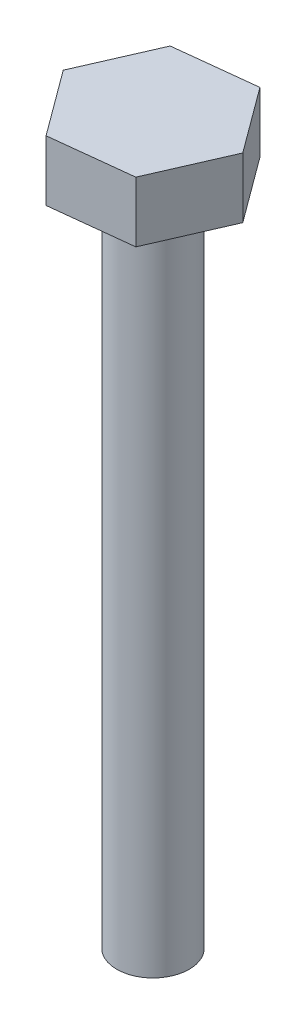
SolidWorks part; units mm, degrees
ref_plane "Front Plane" through (0, 0, 0) normal (0, 0, 1) x (1, 0, 0)
ref_plane "Top Plane" through (0, 0, 0) normal (0, 1, 0) x (1, 0, 0)
ref_plane "Right Plane" through (0, 0, 0) normal (1, 0, 0) x (0, 0, -1)
sketch "Sketch1" plane through (0, 0, 0) normal (0, 1, 0) x (1, 0, 0)
  line L1 (7.9794, -10.8247) -> (13.3642, 1.498)
  line L2 (13.3642, 1.498) -> (5.3848, 12.3227)
  line L3 (5.3848, 12.3227) -> (-7.9794, 10.8247)
  line L4 (-7.9794, 10.8247) -> (-13.3642, -1.498)
  line L5 (-13.3642, -1.498) -> (-5.3848, -12.3227)
  line L6 (-5.3848, -12.3227) -> (7.9794, -10.8247)
  circle A1 centre (0, 0) radius 11.6462 construction
extrude "Boss-Extrude1" add sketch "Sketch1" along normal blind 10
sketch "Sketch2" plane through (0, 0, 0) normal (0, -1, 0) x (1, 0, 0)
  circle A0 centre (0, 0) radius 6
  dimension "D1" = 12
extrude "Boss-Extrude2" add sketch "Sketch2" along normal blind 110
